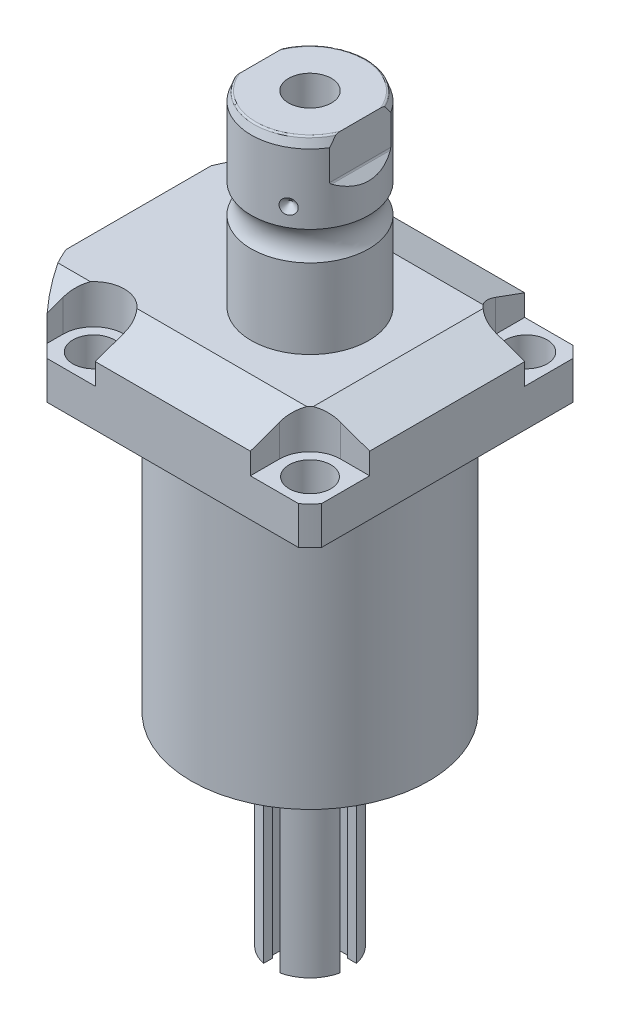
SolidWorks part; units mm, degrees
material "Alloy Steel"
ref_plane "Front Plane" through (0, 0, 0) normal (0, 0, 1) x (1, 0, 0)
ref_plane "Top Plane" through (0, 0, 0) normal (0, 1, 0) x (1, 0, 0)
ref_plane "Right Plane" through (0, 0, 0) normal (1, 0, 0) x (0, 0, -1)
ref_plane "Plane1" through (0, 0, 0) normal (0, 1, 0) x (0, 0, 1)
sketch "Sketch1" plane through (0, 0, 0) normal (0, 1, 0) x (0, 0, 1)
  line L0 (-44.45, 44.45) -> (44.45, 44.45)
  line L1 (44.45, 44.45) -> (44.45, -55.5498)
  line L2 (44.45, -55.5498) -> (-44.45, -55.5498)
  line L3 (-44.45, -55.5498) -> (-44.45, 44.45)
  line L4 (0, 0) -> (0, -60.6467) construction
  dimension "D1" = 55.5498
  dimension "D2" = 99.9998
  dimension "D3" = 88.9
extrude "Extrude1" add sketch "Sketch1" along normal blind 113.919
sketch "Sketch2" plane through (0, 0, 0) normal (0, -1, 0) x (1, 0, 0)
  circle A0 centre (0, 0) radius 60.325
  dimension "D1" = 120.65
extrude "Cut-Extrude1" cut sketch "Sketch2" against normal through all flip side to cut
ref_plane "Plane2" through (0, 0, 0) normal (1, 0, 0) x (0, 0, 1)
sketch "Sketch3" plane through (0, 0, 0) normal (1, 0, 0) x (0, 0, 1)
  line L0 (38.4937, 0) -> (38.4937, -88.9)
  line L1 (38.4937, -88.9) -> (76.5937, -88.9)
  line L2 (76.5937, -88.9) -> (76.5937, 0)
  line L3 (76.5937, 0) -> (38.4937, 0)
  line L4 (0, -93.345) -> (0, 4.445) construction
  line L5 (40.7836, 0) -> (-40.7836, 0) construction
  dimension "D1" = 76.9874
  dimension "D2" = 153.1874
  dimension "D3" = 88.9
revolve "Cut-Revolve1" cut sketch "Sketch3" angle 360 about L4
fillet "Fillet1" radius 0.381 1 edges at (0, 88.9, 38.4937)
sketch "Sketch4" plane through (0, 113.919, 0) normal (0, 1, 0) x (-1, 0, 0)
  line L0 (-44.45, 40.7836) -> (-44.45, -40.7836) construction
  line L1 (40.7836, 44.45) -> (-40.7836, 44.45) construction
  line L2 (-25.1206, -44.45) -> (-25.1206, -35.052)
  line L3 (-44.45, -44.45) -> (-25.1206, -44.45)
  line L4 (-44.45, -25.1206) -> (-44.45, -44.45)
  line L5 (-35.052, -25.1206) -> (-44.45, -25.1206)
  line L6 (44.9834, -44.45) -> (25.1206, -44.45)
  line L7 (25.1206, 44.45) -> (25.1206, 35.052)
  line L8 (44.9834, 44.45) -> (44.9834, 35.052)
  line L9 (44.9834, 44.45) -> (25.1206, 44.45)
  line L10 (-35.052, 25.1206) -> (-44.45, 25.1206)
  line L11 (-44.45, 25.1206) -> (-44.45, 44.45)
  line L12 (-44.45, 44.45) -> (-25.1206, 44.45)
  line L13 (-25.1206, 44.45) -> (-25.1206, 35.052)
  line L14 (-48.9217, 0) -> (49.4551, 0) construction
  line L15 (44.9834, -44.45) -> (44.9834, -35.052)
  line L16 (25.1206, -44.45) -> (25.1206, -35.052)
  arc A0 (25.1206, -35.052) -> (44.9834, -35.052) centre (35.052, -35.052) cw
  arc A1 (-35.052, -25.1206) -> (-25.1206, -35.052) centre (-35.052, -35.052) cw
  arc A2 (-35.052, 25.1206) -> (-25.1206, 35.052) centre (-35.052, 35.052) ccw
  arc A3 (25.1206, 35.052) -> (44.9834, 35.052) centre (35.052, 35.052) ccw
  dimension "D2" = 9.9314
  dimension "D1" = 35.052
  dimension "D3" = 35.052
  dimension "D4" = 35.052
extrude "Cut-Extrude2" cut sketch "Sketch4" against normal blind 12.7
ref_plane "Plane3" through (0, 0, 0) normal (1, 0, 0) x (0, 0, -1)
sketch "Sketch5" plane through (0, 0, 0) normal (1, 0, 0) x (0, 0, -1)
  line L0 (-28.575, 113.919) -> (-44.45, 108.141)
  line L1 (0, 0) -> (0, 154.1081) construction
  line L2 (-28.575, 113.919) -> (-44.45, 113.919)
  line L3 (-44.45, 113.919) -> (-44.45, 108.141)
  dimension "D1" = 15.875
  dimension "D2" = 20
extrude "Cut-Extrude9" cut sketch "Sketch5" against normal through all and the other way through all
mirror "Mirror1" about plane through (0, 0, 0) normal (0, 0, 1) of "Cut-Extrude9"
ref_plane "Plane7" through (0, 0, 0) normal (0, 0, 1) x (1, 0, 0)
sketch "Sketch9" plane through (0, 0, 0) normal (0, 0, 1) x (1, 0, 0)
  line L0 (28.575, 113.919) -> (44.45, 108.141)
  line L1 (44.45, 108.141) -> (44.45, 113.919)
  line L2 (44.45, 113.919) -> (28.575, 113.919)
  dimension "D1" = 15.875
  dimension "D2" = 20
extrude "Cut-Extrude7" cut sketch "Sketch9" against normal through all and the other way through all
ref_plane "Plane8" through (-41.402, 88.9, -18.1102) normal (1, 0, 0) x (0, 1, 0)
sketch "Sketch20" plane through (-41.402, 88.9, -18.1102) normal (1, 0, 0) x (0, 1, 0)
  line L0 (-88.9, 18.1102) -> (39.8401, 18.1102) construction
  line L1 (-7.2797, 36.2204) -> (36.9042, 36.2204) construction
  line L2 (0, 41.9227) -> (1.4478, 41.9227)
  line L3 (0, 58.8938) -> (0, -22.6734) construction
  line L4 (1.4478, 41.9227) -> (1.4478, 39.4716)
  line L5 (1.4478, 39.4716) -> (2.4638, 39.4716)
  line L6 (2.4638, 39.4716) -> (2.4638, 37.465)
  line L7 (2.4638, 37.465) -> (13.4366, 37.465)
  line L8 (13.4366, 37.465) -> (13.4366, 36.2204)
  line L9 (13.4366, 36.2204) -> (0, 36.2204)
  line L10 (0, 41.9227) -> (0, 36.2204)
  dimension "D1" = 18.1102
  dimension "D2" = 11.4046
  dimension "D3" = 1.4478
  dimension "D4" = 6.5024
  dimension "D5" = 1.016
  dimension "D6" = 2.4892
  dimension "D7" = 10.9728
revolve "Cut-Revolve4" cut sketch "Sketch20" angle 360 about L1
mirror "Mirror10" about plane through (0, 0, 0) normal (0, 0, 1) of "Cut-Revolve4"
sketch "Sketch10" plane through (-41.402, 88.9, -18.1102) normal (1, 0, 0) x (0, 1, 0)
  line L0 (-1.0325, 0) -> (1.5659, 0) construction
  line L1 (13.4366, 1.2446) -> (2.4638, 1.2446) construction
  line L2 (2.4638, -1.2446) -> (13.4366, -1.2446) construction
  line L3 (0, 58.8938) -> (0, -22.6734) construction
  circle A0 centre (0.2667, 4.5212) radius 1.1811
  dimension "D1" = 2.3622
  dimension "D2" = 0.2667
  dimension "D3" = 9.0424
revolve "Revolve4" add sketch "Sketch10" angle 360 about L0
ref_plane "Plane9" through (-41.402, 88.9, 18.1102) normal (1, 0, 0) x (0, 1, 0)
sketch "Sketch11" plane through (-41.402, 88.9, 18.1102) normal (1, 0, 0) x (0, 1, 0)
  line L0 (-1.0325, 0) -> (1.5659, 0) construction
  line L1 (13.4366, 1.2446) -> (2.4638, 1.2446) construction
  line L3 (0, 22.6734) -> (0, -58.8938) construction
  line L4 (2.4638, -1.2446) -> (13.4366, -1.2446) construction
  circle A0 centre (0.2667, 4.5212) radius 1.1811
  dimension "D1" = 2.3622
  dimension "D2" = 9.0424
  dimension "D3" = 0.2667
revolve "Revolve2" add sketch "Sketch11" angle 360 about L0
ref_plane "Plane10" through (-55.5498, 101.9048, 12.9794) normal (0, 0, 1) x (0, 1, 0)
sketch "S2D0007" plane through (-55.5498, 101.9048, 12.9794) normal (0, 0, 1) x (0, 1, 0)
  line L0 (0, 0) -> (10.4775, 0)
  line L1 (10.4775, 0) -> (10.4775, -0.254)
  line L2 (10.4775, -0.254) -> (6.1849, -0.254)
  line L3 (6.1849, -0.254) -> (5.6423, -2.8067)
  line L4 (5.6423, -2.8067) -> (4.9784, -3.4706)
  line L5 (4.9784, -3.4706) -> (4.9784, -14.224)
  line L6 (4.9784, -14.224) -> (0, -14.224)
  line L7 (0, -14.224) -> (0, 0)
  line L8 (0, -14.9352) -> (0, 0.7112) construction
  line L9 (-13.0048, 0) -> (-13.0048, -14.7662) construction
  dimension "D1" = 0.254
  dimension "D2" = 13.0048
revolve "Cut-Revolve2" cut sketch "S2D0007" angle 360 about L8
ref_plane "Plane11" through (-55.5498, 101.9048, -12.9794) normal (0, 0, 1) x (0, 1, 0)
sketch "Sketch13" plane through (-55.5498, 101.9048, -12.9794) normal (0, 0, 1) x (0, 1, 0)
  line L0 (0, 0) -> (10.4775, 0)
  line L1 (10.4775, 0) -> (10.4775, -0.254)
  line L2 (10.4775, -0.254) -> (6.1849, -0.254)
  line L3 (6.1849, -0.254) -> (5.6423, -2.8067)
  line L4 (5.6423, -2.8067) -> (4.9784, -3.4706)
  line L5 (4.9784, -3.4706) -> (4.9784, -14.224)
  line L6 (4.9784, -14.224) -> (0, -14.224)
  line L7 (0, -14.224) -> (0, 0)
  line L8 (0, -14.9352) -> (0, 0.7112) construction
  line L9 (-13.0048, 0) -> (-13.0048, -14.7662) construction
  dimension "D1" = 0.254
  dimension "D2" = 13.0048
revolve "Cut-Revolve3" cut sketch "Sketch13" angle 360 about L8
ref_plane "Plane12" through (0, 0, 0) normal (1, 0, 0) x (0, -1, 0)
sketch "Sketch15" plane through (0, 0, 0) normal (1, 0, 0) x (0, -1, 0)
  line L0 (-113.919, 0) -> (-113.919, 19.05)
  line L1 (-113.919, 19.05) -> (-139.6411, 19.05)
  line L2 (-149.0553, 19.05) -> (-171.6024, 19.05)
  line L3 (-174.5234, 17.9868) -> (-174.5234, 0)
  line L4 (-174.5234, 0) -> (-113.919, 0)
  line L5 (-197.6361, 0) -> (-64.6704, 0) construction
  line L6 (-113.919, 27.5233) -> (-113.919, -27.5233) construction
  line L7 (-88.9, 40.7836) -> (-88.9, 44.45) construction
  line L8 (-174.5234, 17.9868) -> (-171.6024, 19.05)
  arc A0 (-149.0553, 19.05) -> (-139.6411, 19.05) centre (-144.3482, 25.4254) ccw
  dimension "D2" = 20
  dimension "D4" = 7.9248
  dimension "D6" = 35.0012
  dimension "D1" = 85.6234
  dimension "D3" = 38.1
  dimension "D5" = 30.1752
  dimension "D7" = 2.921
revolve "Revolve3" add sketch "Sketch15" angle 360 about L5
ref_plane "Plane13" through (0, 0, 0) normal (0, 0, -1) x (0, -1, 0)
sketch "Sketch16" plane through (0, 0, 0) normal (0, 0, -1) x (0, -1, 0)
  line L0 (-174.5234, 19.05) -> (-158.7392, 19.05)
  line L1 (-174.5234, -19.05) -> (-174.5234, -16.2814)
  line L2 (-174.5234, 16.2814) -> (-161.8234, 16.2814)
  line L3 (-161.2846, 16.5046) -> (-158.7392, 19.05)
  line L4 (-161.2846, -16.5046) -> (-158.7392, -19.05)
  line L5 (-174.5234, -16.2814) -> (-161.8234, -16.2814)
  line L6 (-174.5234, 19.05) -> (-174.5234, 16.2814)
  line L7 (-174.5234, -19.05) -> (-158.7392, -19.05)
  line L8 (-194.0458, 0) -> (-125.0021, 0) construction
  line L11 (-174.5234, 17.9868) -> (-174.5234, -17.9868) construction
  line L12 (-149.0553, 19.05) -> (-171.6024, 19.05) construction
  arc A0 (-161.8234, 16.2814) -> (-161.2846, 16.5046) centre (-161.8234, 17.0434) ccw
  arc A1 (-161.8234, -16.2814) -> (-161.2846, -16.5046) centre (-161.8234, -17.0434) cw
  point P3 (-161.5078, 16.2814)
  dimension "D4" = 0.762
  dimension "D1" = 32.5628
  dimension "D2" = 45
  dimension "D3" = 12.7
extrude "Cut-Extrude8" cut sketch "Sketch16" against normal mid plane 106.68
hole_wizard "Hole1" positions "Sketch18" profile "Sketch17" legacy end condition up to next
sketch "Sketch18" plane through (0, 101.219, 0) normal (0, 1, 0) x (-1, 0, 0)
  arc A0 (44.9834, -35.052) -> (25.1206, -35.052) centre (35.052, -35.052) ccw construction
  arc A1 (25.1206, 35.052) -> (44.9834, 35.052) centre (35.052, 35.052) ccw construction
  arc A2 (-35.052, 25.1206) -> (-25.1206, 35.052) centre (-35.052, 35.052) ccw construction
  arc A3 (-25.1206, -35.052) -> (-35.052, -25.1206) centre (-35.052, -35.052) ccw construction
  point P0 (-35.052, -35.052)
  point P1 (-35.052, 35.052)
  point P3 (35.052, 35.052)
  point P5 (35.052, -35.052)
sketch "Sketch17" plane through (35.052, 101.219, -35.052) normal (1, 0, 0) x (0, 0, 1)
  line L0 (0, 0) -> (0, 12.319)
  line L1 (0, 12.319) -> (6.7437, 12.319)
  line L2 (6.7437, 12.319) -> (6.7437, 0)
  line L3 (6.7437, 0) -> (0, 0)
  line L4 (0, 110) -> (0, -10) construction
  dimension "Diameter" = 13.4874
  dimension "Depth" = 12.319
chamfer "Chamfer1" distance 0.635 angle 45 2 edges at (-41.402, 91.3638, 16.8656) (-41.402, 91.3638, -16.8656)
sketch "Sketch21" plane through (0, 0, 0) normal (0, 0, 1) x (1, 0, 0)
  line L0 (0, 0) -> (0, 194.0957) construction
  line L1 (0, 149.1234) -> (6.9342, 153.2899)
  line L2 (6.9342, 153.2899) -> (6.9342, 174.5234)
  line L4 (6.9342, 174.5234) -> (0, 174.5234)
  line L5 (0, 174.5234) -> (0, 149.1234)
  line L6 (16.2814, 174.5234) -> (-16.2814, 174.5234) construction
  dimension "D1" = 13.8684
  dimension "D2" = 59
  dimension "D3" = 25.4
revolve "Cut-Revolve5" cut sketch "Sketch21" angle 360 about L0
fillet "Fillet2" radius 0.635 2 edges at (0, 174.5234, 17.9868) (0, 174.5234, -17.9868)
sketch "Sketch22" plane through (0, 0, 0) normal (0, 0, 1) x (1, 0, 0)
  line L0 (-37.9974, 155.0162) -> (37.12, 155.0162) construction
  line L1 (-19.05, 157.4292) -> (-16.637, 155.0162)
  line L2 (-16.637, 155.0162) -> (-19.05, 155.0162)
  line L3 (-19.05, 155.0162) -> (-19.05, 157.4292)
  line L4 (-19.05, 158.7392) -> (-19.05, 149.0553) construction
  arc A0 (-19.05, 139.6411) -> (-19.05, 149.0553) centre (-25.4254, 144.3482) ccw construction
  dimension "D2" = 10.668
  dimension "D1" = 4.826
  dimension "D3" = 45
revolve "Cut-Revolve6" cut sketch "Sketch22" angle 360 about L0
pattern_circular "CirPattern1" count 3 over 360 about axis through (0, 197.6361, 0) along (0, 1, 0) of "Cut-Revolve6"
sketch "Sketch23" plane through (0, 0, 0) normal (0, 0, 1) x (1, 0, 0)
  line L0 (0, -1000) -> (0, 49000) construction
  line L1 (0, 0) -> (22.225, 0)
  line L2 (-38.4937, 0) -> (38.4937, 0) construction
  line L3 (22.225, 0) -> (22.225, -2.54)
  line L4 (22.225, -2.54) -> (12.7, -2.54)
  line L5 (12.7, -2.54) -> (12.7, -65.532)
  line L6 (12.7, -65.532) -> (0, -65.532)
  line L7 (0, -65.532) -> (0, 0)
  dimension "D1" = 44.45
  dimension "D2" = 25.4
  dimension "D3" = 2.54
  dimension "D4" = 65.532
revolve "Revolve5" add sketch "Sketch23" angle 360 about L0
sketch "Sketch24" plane through (0, -2.54, 0) normal (0, -1, 0) x (1, 0, 0)
  line L0 (-1000, 0) -> (49000, 0) construction
  line L1 (0, -1000) -> (0, 49000) construction
  line L2 (0, 0) -> (43301.2702, 25000) construction
  line L3 (0, 0) -> (25000, 43301.2702) construction
  circle A0 centre (0, 0) radius 19.431 construction
  circle A1 centre (19.431, 0) radius 1.7272
  circle A2 centre (16.8277, 9.7155) radius 1.7272
  circle A3 centre (9.7155, 16.8277) radius 1.7272
  circle A4 centre (0, 19.431) radius 1.7272
  circle A5 centre (-9.7155, 16.8277) radius 1.7272
  circle A6 centre (-16.8277, 9.7155) radius 1.7272
  circle A7 centre (-19.431, 0) radius 1.7272
  circle A8 centre (-16.8277, -9.7155) radius 1.7272
  circle A9 centre (-9.7155, -16.8277) radius 1.7272
  circle A10 centre (0, -19.431) radius 1.7272
  circle A11 centre (9.7155, -16.8277) radius 1.7272
  circle A12 centre (16.8277, -9.7155) radius 1.7272
  dimension "D3" = 38.862
  dimension "D4" = 3.4544
  dimension "D5" = 3.4544
  dimension "D6" = 3.4544
  dimension "D7" = 3.4544
  dimension "D1" = 30
  dimension "D2" = 30
extrude "Cut-Extrude10" cut sketch "Sketch24" against normal up to surface (2.54 mm away) up to face at (0, 0, -22.225)
sketch "Sketch25" plane through (0, -2.54, 0) normal (0, -1, 0) x (1, 0, 0)
  circle A0 centre (19.431, 0) radius 2.7051
  circle A1 centre (-9.7155, 16.8277) radius 2.7051
  circle A2 centre (-9.7155, -16.8277) radius 2.7051
  dimension "D1" = 5.4102
  dimension "D2" = 5.4102
  dimension "D3" = 5.4102
extrude "Extrude2" add sketch "Sketch25" along normal blind 2.9464
ref_plane "Plane15-slot-angle" through (0, 0, 0) normal (1, 0, 0) x (0, 0, -1)
ref_plane "Plane16" through (0, -34.036, 12.7) normal (0, 0, 1) x (-1, 0, 0)
sketch "Sketch31" plane through (0, -34.036, 12.7) normal (0, 0, 1) x (-1, 0, 0)
  line L0 (0, -1034.036) -> (0, 48965.964) construction
  line L1 (0, -1034.036) -> (0, 48965.964) construction
  line L2 (-2.6416, -21.0834) -> (-2.6416, 31.496)
  line L3 (12.7, 31.496) -> (-12.7, 31.496) construction
  line L4 (-2.6416, 31.496) -> (2.6416, 31.496)
  line L5 (2.6416, -21.0834) -> (2.6416, 31.496)
  arc A0 (-2.6416, -21.0834) -> (2.6416, -21.0834) centre (0, -23.368) ccw
  point P14 (0, 31.496)
  dimension "D1" = 6.985
  dimension "D2" = 5.2832
  dimension "D3" = 54.864
extrude "Cut-Extrude11" cut sketch "Sketch31" against normal blind 6.477
sketch "Sketch32" plane through (0, 0, 6.223) normal (0, 0, 1) x (1, 0, 0)
  line L0 (0, -1000) -> (0, 49000) construction
  line L1 (3.4925, -10.668) -> (3.4925, -65.532)
  line L2 (-12.7, -65.532) -> (12.7, -65.532) construction
  line L3 (3.4925, -65.532) -> (-3.4925, -65.532)
  line L4 (-2.6416, -65.532) -> (2.6416, -65.532) construction
  line L5 (3.4925, -10.668) -> (-3.4925, -10.668)
  line L6 (-3.4925, -10.668) -> (-3.4925, -65.532)
  point P13 (0, -65.532)
  point P14 (0, -10.668)
  dimension "D1" = 6.985
extrude "Cut-Extrude12" cut sketch "Sketch32" along normal blind 3.302
ref_plane "Plane17" through (0, 0, 0) normal (0, 0, 1) x (1, 0, 0)
mirror "Mirror11" about plane through (0, 0, 0) normal (0, 0, 1) of "Cut-Extrude11", "Cut-Extrude12"
sketch "Sketch35" plane through (0, -5.4864, 0) normal (0, -1, 0) x (1, 0, 0)
  line L1 (19.431, -1.4371) -> (20.6756, -0.7186)
  line L2 (20.6756, -0.7186) -> (20.6756, 0.7186)
  line L3 (20.6756, 0.7186) -> (19.431, 1.4371)
  line L4 (19.431, 1.4371) -> (18.1864, 0.7186)
  line L5 (18.1864, 0.7186) -> (18.1864, -0.7186)
  line L6 (18.1864, -0.7186) -> (19.431, -1.4371)
  line L7 (-9.2553, 15.4663) -> (-8.3063, 16.5455)
  line L8 (-8.3063, 16.5455) -> (-8.7665, 17.907)
  line L9 (-8.7665, 17.907) -> (-10.1757, 18.1892)
  line L10 (-10.1757, 18.1892) -> (-11.1247, 17.1099)
  line L11 (-11.1247, 17.1099) -> (-10.6645, 15.7485)
  line L12 (-10.6645, 15.7485) -> (-9.2553, 15.4663)
  line L13 (-9.7155, -18.2649) -> (-8.4709, -17.5463)
  line L14 (-8.4709, -17.5463) -> (-8.4709, -16.1092)
  line L15 (-8.4709, -16.1092) -> (-9.7155, -15.3906)
  line L16 (-9.7155, -15.3906) -> (-10.9601, -16.1092)
  line L17 (-10.9601, -16.1092) -> (-10.9601, -17.5463)
  line L18 (-10.9601, -17.5463) -> (-9.7155, -18.2649)
  circle A0 centre (19.431, 0) radius 1.2446 construction
  circle A1 centre (-9.7155, 16.8277) radius 1.2446 construction
  circle A2 centre (-9.7155, -16.8277) radius 1.2446 construction
  dimension "D1" = 2.4892
  dimension "D2" = 2.4892
  dimension "D3" = 2.4892
extrude "Cut-Extrude13" cut sketch "Sketch35" against normal blind 2.032
pattern_circular "CirPattern2" count 2 every 90 about axis through (0, 0, 0) along (0, 1, 0) of "Mirror11", "Cut-Extrude11", "Cut-Extrude12"
